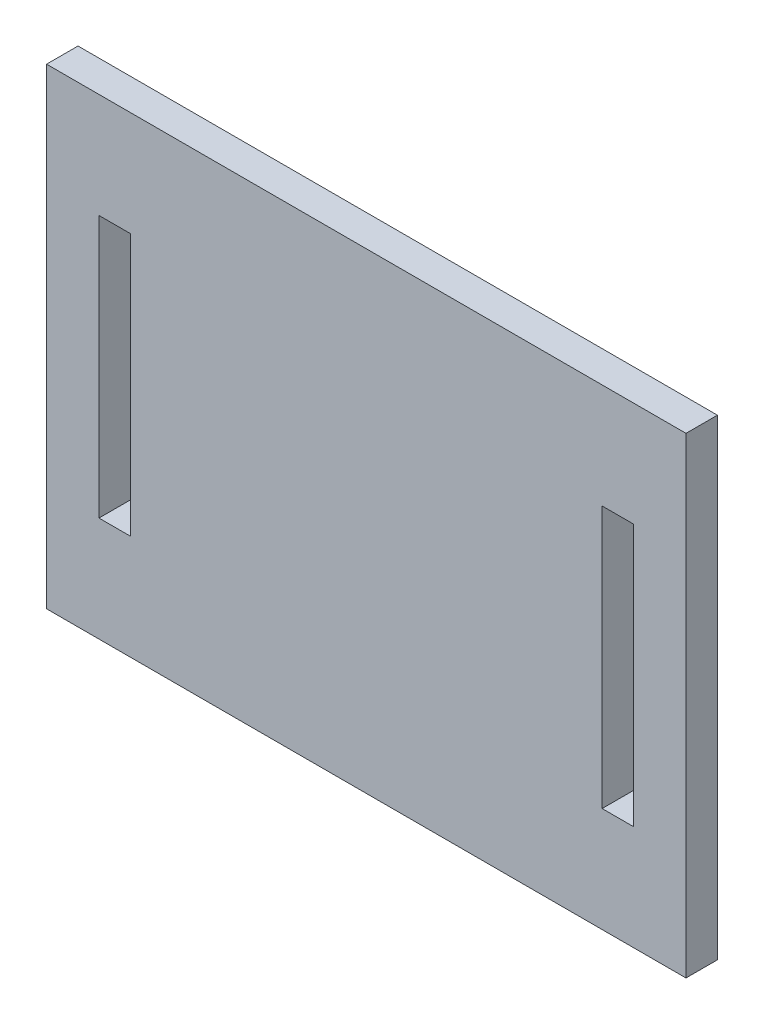
SolidWorks part; units mm, degrees
ref_plane "Plano frontal" through (0, 0, 0) normal (0, 0, 1) x (1, 0, 0)
ref_plane "Plano superior" through (0, 0, 0) normal (0, 1, 0) x (1, 0, 0)
ref_plane "Plano direito" through (0, 0, 0) normal (1, 0, 0) x (0, 0, -1)
sketch "Esboço1" plane through (0, 0, 0) normal (0, 0, 1) x (1, 0, 0)
  line L1 (-33.3215, 14.7917) -> (27.6785, 14.7917)
  line L2 (-33.3215, 14.7917) -> (-33.3215, -30.2083)
  line L3 (-33.3215, -30.2083) -> (27.6785, -30.2083)
  line L4 (27.6785, 14.7917) -> (27.6785, -30.2083)
  dimension "D1" = 61
  dimension "D2" = 45
extrude "Ressalto-extrusão1" add sketch "Esboço1" along normal blind 3
sketch "Esboço3" plane through (0, 0, 3) normal (0, 0, 1) x (1, 0, 0)
  line L0 (-33.3215, 14.7917) -> (-33.3215, -30.2083) construction
  line L1 (-28.3215, -20.2083) -> (-25.3215, -20.2083)
  line L2 (-28.3215, -20.2083) -> (-28.3215, 4.7917)
  line L3 (-28.3215, 4.7917) -> (-25.3215, 4.7917)
  line L4 (-25.3215, -20.2083) -> (-25.3215, 4.7917)
  line L5 (-33.3215, -30.2083) -> (27.6785, -30.2083) construction
  line L6 (27.6785, -30.2083) -> (27.6785, 14.7917) construction
  line L7 (19.6785, -20.2083) -> (22.6785, -20.2083)
  line L8 (19.6785, -20.2083) -> (19.6785, 4.7917)
  line L9 (19.6785, 4.7917) -> (22.6785, 4.7917)
  line L10 (22.6785, -20.2083) -> (22.6785, 4.7917)
  dimension "D1" = 25
  dimension "D2" = 3
  dimension "D3" = 5
  dimension "D4" = 10
  dimension "D5" = 10
  dimension "D6" = 25
  dimension "D7" = 5
  dimension "D8" = 3
extrude "Corte-extrusão1" cut sketch "Esboço3" against normal blind 3
